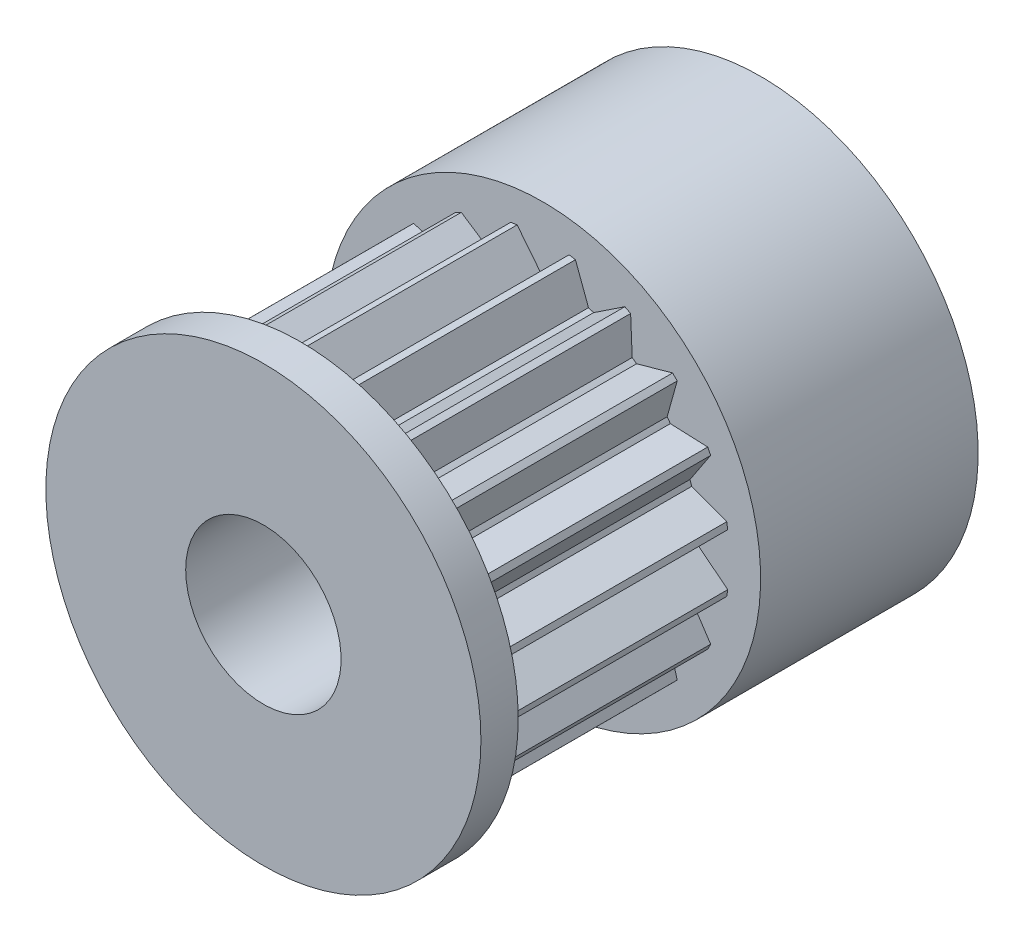
SolidWorks part; units mm, degrees
ref_plane "前视" through (0, 0, 0) normal (0, 0, 1) x (1, 0, 0)
ref_plane "上视" through (0, 0, 0) normal (0, 1, 0) x (1, 0, 0)
ref_plane "右视" through (0, 0, 0) normal (1, 0, 0) x (0, 0, -1)
sketch "草图1" plane through (0, 0, 0) normal (0, 0, 1) x (1, 0, 0)
  line L0 (0, 0) -> (50000, 0) construction
  line L1 (0, 0) -> (8.4992, 0.1484) construction
  line L2 (0.0658, 0.0104) -> (49384.4829, 7821.7337) construction
  line L3 (4.9992, -0.0873) -> (5.9416, -0.835)
  line L4 (5.9088, -1.0419) -> (4.7815, -1.4619)
  line L5 (4.7276, -1.6278) -> (5.3928, -2.6302)
  line L6 (5.2977, -2.8168) -> (4.0958, -2.8679)
  line L7 (3.9932, -3.0091) -> (4.316, -4.168)
  line L8 (4.168, -4.316) -> (3.0091, -3.9932)
  line L9 (4.7815, 1.4619) -> (5.9088, 1.0419)
  line L10 (5.9416, 0.835) -> (4.9992, 0.0873)
  line L11 (2.8679, -4.0958) -> (2.8168, -5.2977)
  line L12 (2.6302, -5.3928) -> (1.6278, -4.7276)
  line L13 (1.4619, -4.7815) -> (1.0419, -5.9088)
  line L14 (0.835, -5.9416) -> (0.0873, -4.9992)
  line L15 (-0.0873, -4.9992) -> (-0.835, -5.9416)
  line L16 (-1.0419, -5.9088) -> (-1.4619, -4.7815)
  line L17 (-1.6278, -4.7276) -> (-2.6302, -5.3928)
  line L18 (-2.8168, -5.2977) -> (-2.8679, -4.0958)
  line L19 (-3.0091, -3.9932) -> (-4.168, -4.316)
  line L20 (-4.316, -4.168) -> (-3.9932, -3.0091)
  line L21 (-4.0958, -2.8679) -> (-5.2977, -2.8168)
  line L22 (-5.3928, -2.6302) -> (-4.7276, -1.6278)
  line L23 (-4.7815, -1.4619) -> (-5.9088, -1.0419)
  line L24 (-5.9416, -0.835) -> (-4.9992, -0.0873)
  line L25 (-4.9992, 0.0873) -> (-5.9416, 0.835)
  line L26 (-5.9088, 1.0419) -> (-4.7815, 1.4619)
  line L27 (-4.7276, 1.6278) -> (-5.3928, 2.6302)
  line L28 (-5.2977, 2.8168) -> (-4.0958, 2.8679)
  line L29 (-3.9932, 3.0091) -> (-4.316, 4.168)
  line L30 (-4.168, 4.316) -> (-3.0091, 3.9932)
  line L31 (-2.8679, 4.0958) -> (-2.8168, 5.2977)
  line L32 (-2.6302, 5.3928) -> (-1.6278, 4.7276)
  line L33 (-1.4619, 4.7815) -> (-1.0419, 5.9088)
  line L34 (-0.835, 5.9416) -> (-0.0873, 4.9992)
  line L35 (0.0873, 4.9992) -> (0.835, 5.9416)
  line L36 (1.0419, 5.9088) -> (1.4619, 4.7815)
  line L37 (1.6278, 4.7276) -> (2.6302, 5.3928)
  line L38 (2.8168, 5.2977) -> (2.8679, 4.0958)
  line L39 (3.0091, 3.9932) -> (4.168, 4.316)
  line L40 (4.316, 4.168) -> (3.9932, 3.0091)
  line L41 (4.0958, 2.8679) -> (5.2977, 2.8168)
  line L42 (5.3928, 2.6302) -> (4.7276, 1.6278)
  circle A0 centre (0, 0) radius 5 construction
  arc A1 (4.9992, -0.0873) -> (4.9992, 0.0873) centre (0, 0) ccw
  arc A2 (4.7815, 1.4619) -> (4.7276, 1.6278) centre (0, 0) ccw
  arc A3 (5.9088, -1.0419) -> (5.9416, -0.835) centre (0, 0) ccw
  arc A4 (5.9416, 0.835) -> (5.9088, 1.0419) centre (0, 0) ccw
  arc A5 (4.7276, -1.6278) -> (4.7815, -1.4619) centre (0, 0) ccw
  arc A6 (5.2977, -2.8168) -> (5.3928, -2.6302) centre (0, 0) ccw
  arc A7 (3.9932, -3.0091) -> (4.0958, -2.8679) centre (0, 0) ccw
  arc A8 (4.168, -4.316) -> (4.316, -4.168) centre (0, 0) ccw
  arc A9 (2.8679, -4.0958) -> (3.0091, -3.9932) centre (0, 0) ccw
  arc A10 (2.6302, -5.3928) -> (2.8168, -5.2977) centre (0, 0) ccw
  arc A11 (1.4619, -4.7815) -> (1.6278, -4.7276) centre (0, 0) ccw
  arc A12 (0.835, -5.9416) -> (1.0419, -5.9088) centre (0, 0) ccw
  arc A13 (-0.0873, -4.9992) -> (0.0873, -4.9992) centre (0, 0) ccw
  arc A14 (-1.0419, -5.9088) -> (-0.835, -5.9416) centre (0, 0) ccw
  arc A15 (-1.6278, -4.7276) -> (-1.4619, -4.7815) centre (0, 0) ccw
  arc A16 (-2.8168, -5.2977) -> (-2.6302, -5.3928) centre (0, 0) ccw
  arc A17 (-3.0091, -3.9932) -> (-2.8679, -4.0958) centre (0, 0) ccw
  arc A18 (-4.316, -4.168) -> (-4.168, -4.316) centre (0, 0) ccw
  arc A19 (-4.0958, -2.8679) -> (-3.9932, -3.0091) centre (0, 0) ccw
  arc A20 (-5.3928, -2.6302) -> (-5.2977, -2.8168) centre (0, 0) ccw
  arc A21 (-4.7815, -1.4619) -> (-4.7276, -1.6278) centre (0, 0) ccw
  arc A22 (-5.9416, -0.835) -> (-5.9088, -1.0419) centre (0, 0) ccw
  arc A23 (-4.9992, 0.0873) -> (-4.9992, -0.0873) centre (0, 0) ccw
  arc A24 (-5.9088, 1.0419) -> (-5.9416, 0.835) centre (0, 0) ccw
  arc A25 (-4.7276, 1.6278) -> (-4.7815, 1.4619) centre (0, 0) ccw
  arc A26 (-5.2977, 2.8168) -> (-5.3928, 2.6302) centre (0, 0) ccw
  arc A27 (-3.9932, 3.0091) -> (-4.0958, 2.8679) centre (0, 0) ccw
  arc A28 (-4.168, 4.316) -> (-4.316, 4.168) centre (0, 0) ccw
  arc A29 (-2.8679, 4.0958) -> (-3.0091, 3.9932) centre (0, 0) ccw
  arc A30 (-2.6302, 5.3928) -> (-2.8168, 5.2977) centre (0, 0) ccw
  arc A31 (-1.4619, 4.7815) -> (-1.6278, 4.7276) centre (0, 0) ccw
  arc A32 (-0.835, 5.9416) -> (-1.0419, 5.9088) centre (0, 0) ccw
  arc A33 (0.0873, 4.9992) -> (-0.0873, 4.9992) centre (0, 0) ccw
  arc A34 (1.0419, 5.9088) -> (0.835, 5.9416) centre (0, 0) ccw
  arc A35 (1.6278, 4.7276) -> (1.4619, 4.7815) centre (0, 0) ccw
  arc A36 (2.8168, 5.2977) -> (2.6302, 5.3928) centre (0, 0) ccw
  arc A37 (3.0091, 3.9932) -> (2.8679, 4.0958) centre (0, 0) ccw
  arc A38 (4.316, 4.168) -> (4.168, 4.316) centre (0, 0) ccw
  arc A39 (4.0958, 2.8679) -> (3.9932, 3.0091) centre (0, 0) ccw
  arc A40 (5.3928, 2.6302) -> (5.2977, 2.8168) centre (0, 0) ccw
  point P112 (0, 0)
  dimension "D2" = 6
  dimension "D5" = 29.432
  dimension "D1" = 5
  dimension "D3" = 0.2094
  dimension "D6" = 0.1745
  dimension "D4" = 1
  dimension "D7" = 9
  dimension "D8" = 20
extrude "凸台-拉伸1" add sketch "草图1" along normal blind 7.8
sketch "草图2" plane through (0, 0, 7.8) normal (0, 0, 1) x (1, 0, 0)
  circle A0 centre (0, 0) radius 7
  dimension "D1" = 14
extrude "凸台-拉伸2" add sketch "草图2" along normal blind 1.2
sketch "草图3" plane through (0, 0, 0) normal (0, 0, -1) x (-1, 0, 0)
  circle A0 centre (0, 0) radius 7
  dimension "D1" = 14
extrude "凸台-拉伸3" add sketch "草图3" along normal blind 7
sketch "草图4" plane through (0, 0, -7) normal (0, 0, -1) x (-1, 0, 0)
  circle A0 centre (0, 0) radius 2.5
  dimension "D1" = 5
extrude "切除-拉伸1" cut sketch "草图4" against normal through all
sketch "草图6" plane through (0, 0, 0) normal (0, 1, 0) x (1, 0, 0)
  line L0 (0, 0) -> (0, 50000) construction
  circle A0 centre (0, 3.5) radius 2
  dimension "D1" = 4
  dimension "D2" = 3.5
extrude "切除-拉伸2" cut sketch "草图6" against normal through all
sketch "草图7" plane through (0, 0, 0) normal (1, 0, 0) x (0, 0, -1)
  line L0 (0, 0) -> (50000, 0) construction
  line L1 (0, 7) -> (0, -7) construction
  circle A0 centre (3.5, 0) radius 2
  dimension "D1" = 4
  dimension "D2" = 3.5
extrude "切除-拉伸3" cut sketch "草图7" against normal through all
